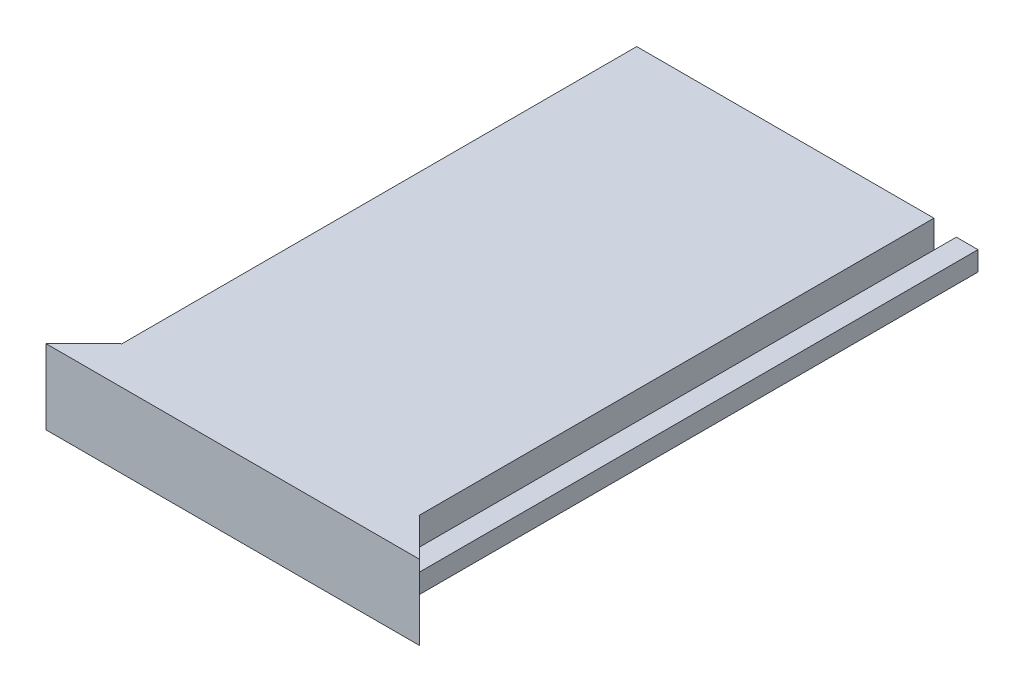
SolidWorks part; units mm, degrees
ref_plane "Front Plane" through (0, 0, 0) normal (0, 0, 1) x (1, 0, 0)
ref_plane "Top Plane" through (0, 0, 0) normal (0, 1, 0) x (1, 0, 0)
ref_plane "Right Plane" through (0, 0, 0) normal (1, 0, 0) x (0, 0, -1)
sketch "Sketch1" plane through (0, 0, 0) normal (0, 0, 1) x (1, 0, 0)
  line L1 (-25, 5) -> (25, 5)
  line L2 (-25, 5) -> (-25, -5)
  line L3 (-25, -5) -> (25, -5)
  line L4 (25, 5) -> (25, -5)
  line L5 (-25, 5) -> (25, -5) construction
  line L6 (-25, -5) -> (25, 5) construction
  point P0 (0, 0)
  dimension "D1" = 10
  dimension "D2" = 50
extrude "Boss-Extrude1" add sketch "Sketch1" along normal blind 5
sketch "Sketch2" plane through (0, 0, 0) normal (0, 1, 0) x (1, 0, 0)
  line L0 (-25, -5) -> (-20, 0)
  line L1 (25, -5) -> (20, 0)
  line L2 (25, -5) -> (-25, -5) construction
  line L3 (-25, -5) -> (-25, 0) construction
  line L4 (-25, -5) -> (-25, 0)
  line L5 (25, 0) -> (-25, 0) construction
  line L6 (25, 0) -> (20, 0)
  line L7 (25, -5) -> (25, 0) construction
  line L8 (25, -5) -> (25, 0)
  line L9 (-20, 0) -> (-25, 0)
  dimension "D1" = 45
  dimension "D2" = 45
extrude "Cut-Extrude1" cut sketch "Sketch2" against normal through all both and the other way through all
sketch "Sketch3" plane through (0, 0, 5) normal (0, 0, 1) x (1, 0, 0)
  line L0 (-25, 0) -> (25, 0) construction
  line L1 (-25, 5) -> (-25, -5) construction
  line L2 (25, -5) -> (25, 5) construction
  line L4 (-22.8, 1.3) -> (22.8, 1.3)
  line L5 (-22.8, 1.3) -> (-22.8, -1.3)
  line L6 (-22.8, -1.3) -> (22.8, -1.3)
  line L7 (22.8, 1.3) -> (22.8, -1.3)
  dimension "D1" = 2.2
  dimension "D2" = 2.2
  dimension "D3" = 2.6
  dimension "D4" = 1.3
extrude "Boss-Extrude2" add sketch "Sketch3" against normal blind 77
sketch "Sketch4" plane through (0, 1.3, 0) normal (0, 1, 0) x (1, 0, 0)
  line L8 (20, 0) -> (-20, 0) construction
  line L9 (-19.9, 0) -> (19.9, 0)
  line L10 (-19.9, 0) -> (-19.9, 72)
  line L11 (-19.9, 72) -> (19.9, 72)
  line L12 (19.9, 0) -> (19.9, 72)
  line L13 (22.8, 72) -> (-22.8, 72) construction
  line L14 (22.8, 72) -> (22.8, -2.8) construction
  line L15 (-22.8, 72) -> (-22.8, -2.8) construction
  dimension "D1" = 2.9
  dimension "D2" = 2.9
extrude "Cut-Extrude2" cut sketch "Sketch4" against normal blind 77
sketch "Sketch6" plane through (0, 0, 0) normal (0, 0, -1) x (-1, 0, 0)
  line L2 (-19.9, -1.3) -> (-19.9, 5)
  line L4 (-18.4, -1.3) -> (-18.4, 3)
  line L5 (-19.9, 5) -> (19.9, 5)
  line L7 (19.9, -1.3) -> (19.9, 5)
  line L9 (18.4, -1.3) -> (18.4, 3)
  line L12 (-18.4, 3) -> (18.4, 3)
  line L14 (18.4, -1.3) -> (19.9, -1.3)
  line L15 (-19.9, -1.3) -> (-18.4, -1.3)
extrude "Boss-Extrude3" add sketch "Sketch6" along normal up to surface (72 mm away) up to face at (21.35, 0, -72)
sketch "Sketch7" plane through (0, 5, 0) normal (0, 1, 0) x (1, 0, 0)
  line L0 (19.9, 0) -> (19.9, 72) construction
  line L1 (-19.9, 72) -> (19.9, 72)
  line L2 (-19.9, 72) -> (-19.9, 69)
  line L3 (-19.9, 69) -> (19.9, 69)
  line L4 (19.9, 72) -> (19.9, 69)
  dimension "D1" = 3
extrude "Cut-Extrude3" cut sketch "Sketch7" against normal blind 10
